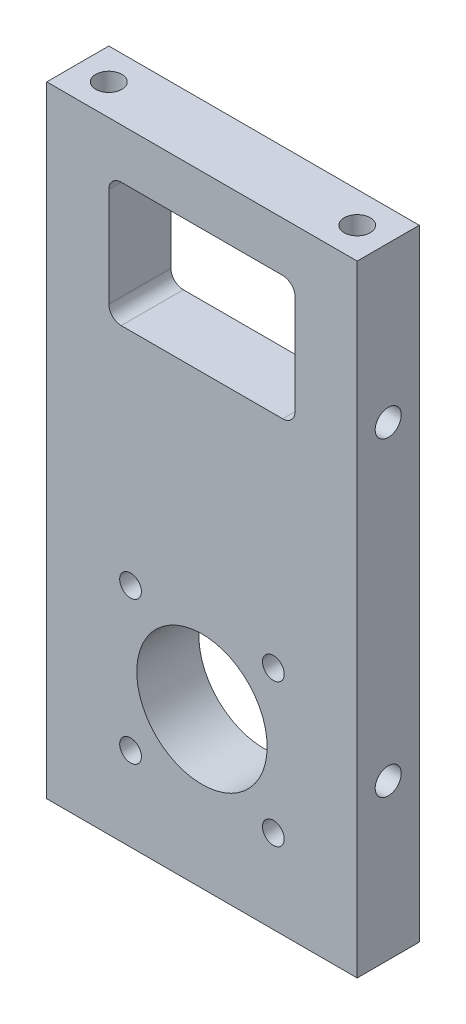
SolidWorks part; units mm, degrees
ref_plane "Front Plane" through (0, 0, 0) normal (0, 0, 1) x (1, 0, 0)
ref_plane "Top Plane" through (0, 0, 0) normal (0, 1, 0) x (1, 0, 0)
ref_plane "Right Plane" through (0, 0, 0) normal (1, 0, 0) x (0, 0, -1)
sketch "Sketch1" plane through (0, 0, 0) normal (0, 1, 0) x (1, 0, 0)
  line L0 (-26.0517, -410.1922) -> (-26.0517, 40.8078) construction
  line L1 (-26.0517, -394.6922) -> (23.9483, -394.6922)
  line L2 (-26.0517, -394.6922) -> (-26.0517, -384.6922)
  line L3 (-26.0517, -384.6922) -> (23.9483, -384.6922)
  line L4 (23.9483, -394.6922) -> (23.9483, -384.6922)
  line L5 (19.4483, -414.6922) -> (-21.5517, -414.6922) construction
  dimension "D1" = 50
  dimension "D2" = 10
  dimension "D3" = 20
extrude "Boss-Extrude1" add sketch "Sketch1" along normal blind 100
hole_wizard "M5x0.8 Tapped Hole1" positions "Sketch3" profile "Sketch2" tap size "M5x0.8" standard "Ansi Metric"
sketch "Sketch3" plane through (0, 0, 0) normal (0, -1, 0) x (1, 0, 0)
  line L0 (-26.0517, 384.6922) -> (-26.0517, 394.6922) construction
  line L1 (-26.0517, 394.6922) -> (23.9483, 394.6922) construction
  line L2 (23.9483, 394.6922) -> (23.9483, 384.6922) construction
  line L3 (23.9483, 384.6922) -> (-26.0517, 384.6922) construction
  point P0 (18.9483, 389.6922)
  point P1 (-21.0517, 389.6922)
  dimension "D1" = 5
  dimension "D2" = 5
  dimension "D3" = 5
  dimension "D4" = 5
sketch "Sketch2" plane through (18.9483, 0, 389.6922) normal (1, 0, 0) x (0, 0, -1)
  line L0 (0, 0) -> (0, 15.2618)
  line L1 (0, 15.2618) -> (2.1, 14)
  line L2 (2.1, 14) -> (2.1, 0)
  line L5 (2.1, 0) -> (0, 0)
  line L10 (0, 15.2618) -> (-2.1, 14) construction
  line L11 (0, -6.35) -> (0, 107.95) construction
  dimension "Tap Drill Dia." = 4.2
  dimension "Tap Drill Depth" = 14
  dimension "Drill Angle" = 118
cosmetic thread "Hole Thread1" parameters "D1"=10, "D2"=5
cosmetic thread "Hole Thread2" parameters "D1"=10, "D2"=5
hole_wizard "M5x0.8 Tapped Hole2" positions "Sketch5" profile "Sketch4" tap size "M5x0.8" standard "Ansi Metric"
sketch "Sketch5" plane through (0, 100, 0) normal (0, 1, 0) x (-1, 0, 0)
  point P0 (21.0517, 389.6922)
  point P1 (-18.9483, 389.6922)
sketch "Sketch4" plane through (-21.0517, 100, 389.6922) normal (1, 0, 0) x (0, 0, 1)
  line L0 (0, 0) -> (0, 15.2618)
  line L1 (0, 15.2618) -> (2.1, 14)
  line L2 (2.1, 14) -> (2.1, 0)
  line L5 (2.1, 0) -> (0, 0)
  line L10 (0, 15.2618) -> (-2.1, 14) construction
  line L11 (0, -6.35) -> (0, 107.95) construction
  dimension "Tap Drill Dia." = 4.2
  dimension "Tap Drill Depth" = 14
  dimension "Drill Angle" = 118
cosmetic thread "Hole Thread3" parameters "D1"=10, "D2"=5
cosmetic thread "Hole Thread4" parameters "D1"=10, "D2"=5
hole_wizard "M5x0.8 Tapped Hole3" positions "Sketch7" profile "Sketch6" tap size "M5x0.8" standard "Ansi Metric"
sketch "Sketch7" plane through (-26.0517, 0, 0) normal (-1, 0, 0) x (0, 0, 1)
  line L0 (384.6922, 100) -> (394.6922, 100) construction
  line L1 (384.6922, 100) -> (384.6922, 0) construction
  line L2 (384.6922, 0) -> (394.6922, 0) construction
  point P0 (389.6922, 75)
  point P1 (389.6922, 25)
  dimension "D1" = 25
  dimension "D2" = 5
  dimension "D3" = 5
  dimension "D4" = 25
sketch "Sketch6" plane through (-26.0517, 75, 389.6922) normal (0, 1, 0) x (0, 0, 1)
  line L0 (0, 0) -> (0, 9.2618)
  line L1 (0, 9.2618) -> (2.1, 8)
  line L2 (2.1, 8) -> (2.1, 0)
  line L5 (2.1, 0) -> (0, 0)
  line L10 (0, 9.2618) -> (-2.1, 8) construction
  line L11 (0, -6.35) -> (0, 107.95) construction
  dimension "Tap Drill Dia." = 4.2
  dimension "Tap Drill Depth" = 8
  dimension "Drill Angle" = 118
cosmetic thread "Hole Thread5" parameters "D1"=5, "D2"=5
cosmetic thread "Hole Thread6" parameters "D1"=5, "D2"=5
hole_wizard "M5x0.8 Tapped Hole4" positions "Sketch9" profile "Sketch8" tap size "M5x0.8" standard "Ansi Metric"
sketch "Sketch9" plane through (23.9483, 0, 0) normal (1, 0, 0) x (0, 0, -1)
  line L0 (-394.6922, 100) -> (-384.6922, 100) construction
  line L1 (-394.6922, 100) -> (-394.6922, 0) construction
  line L2 (-394.6922, 0) -> (-384.6922, 0) construction
  point P0 (-389.6922, 75)
  point P1 (-389.6922, 25)
  dimension "D1" = 25
  dimension "D2" = 5
  dimension "D3" = 5
  dimension "D4" = 25
sketch "Sketch8" plane through (23.9483, 75, 389.6922) normal (0, 1, 0) x (0, 0, -1)
  line L0 (0, 0) -> (0, 9.2618)
  line L1 (0, 9.2618) -> (2.1, 8)
  line L2 (2.1, 8) -> (2.1, 0)
  line L5 (2.1, 0) -> (0, 0)
  line L10 (0, 9.2618) -> (-2.1, 8) construction
  line L11 (0, -6.35) -> (0, 107.95) construction
  dimension "Tap Drill Dia." = 4.2
  dimension "Tap Drill Depth" = 8
  dimension "Drill Angle" = 118
cosmetic thread "Hole Thread7" parameters "D1"=5, "D2"=5
cosmetic thread "Hole Thread8" parameters "D1"=5, "D2"=5
sketch "Sketch11" plane through (0, 0, 394.6922) normal (0, 0, 1) x (1, 0, 0)
  line L0 (-26.0517, -10) -> (-26.0517, 100) construction
  line L1 (-16.0517, 92) -> (13.9483, 92)
  line L2 (-16.0517, 92) -> (-16.0517, 72)
  line L3 (-16.0517, 72) -> (13.9483, 72)
  line L4 (13.9483, 92) -> (13.9483, 72)
  line L5 (-26.0517, 100) -> (23.9483, 100) construction
  line L6 (23.9483, 100) -> (23.9483, 0) construction
  line L7 (-26.0517, 100) -> (-26.0517, 0) construction
  line L8 (-26.0517, 0) -> (23.9483, 0) construction
  circle A0 centre (-1.0517, 25) radius 10.5
  circle A1 centre (-12.5517, 36.5) radius 1.75
  circle A2 centre (10.4483, 36.5) radius 1.75
  circle A3 centre (10.4483, 13.5) radius 1.75
  circle A4 centre (-12.5517, 13.5) radius 1.75
  dimension "D5" = 21
  dimension "D8" = 3.5
  dimension "D9" = 3.5
  dimension "D10" = 3.5
  dimension "D11" = 3.5
  dimension "D1" = 10
  dimension "D2" = 8
  dimension "D3" = 10
  dimension "D4" = 20
  dimension "D6" = 25
  dimension "D7" = 25
  dimension "D12" = 23
  dimension "D13" = 23
  dimension "D14" = 23
  dimension "D15" = 23
  dimension "D16" = 11.5
  dimension "D17" = 11.5
  dimension "D18" = 11.5
  dimension "D19" = 11.5
extrude "Cut-Extrude2" cut sketch "Sketch11" against normal up to next
fillet "Fillet2" radius 2 4 edges at (13.9483, 72, 389.6922) (13.9483, 92, 389.6922) (-16.0517, 92, 389.6922) (-16.0517, 72, 389.6922)
